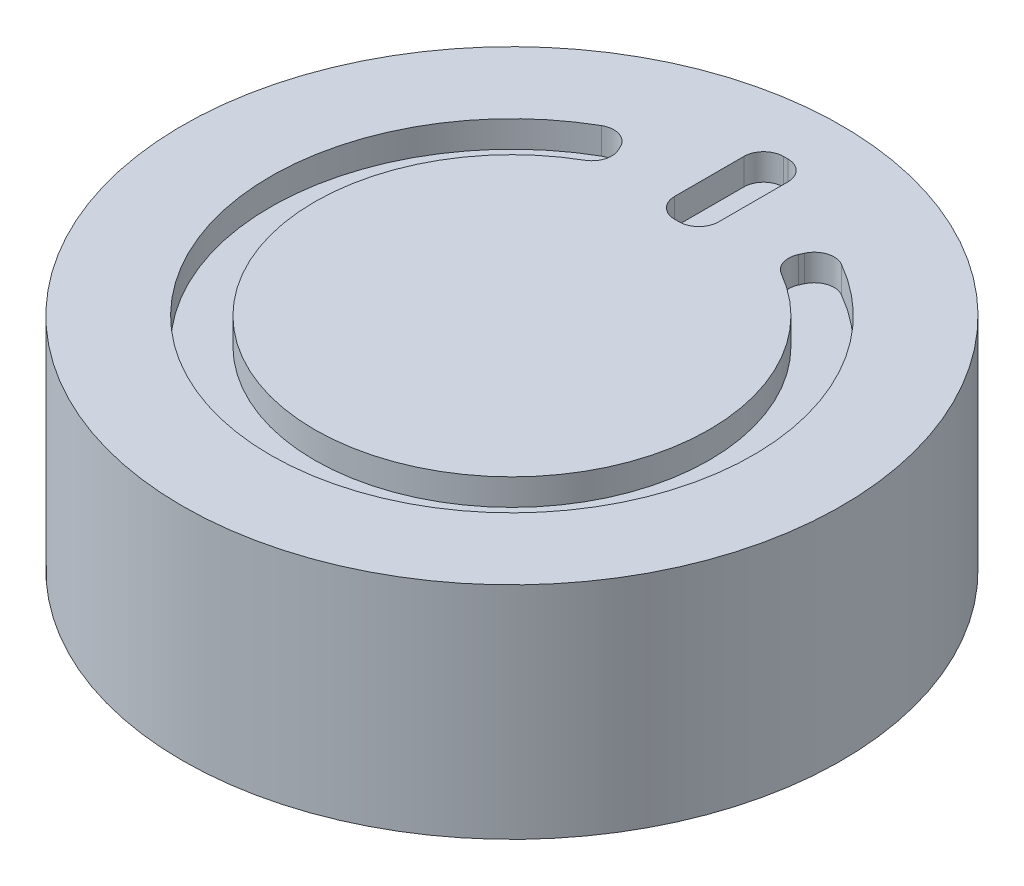
SolidWorks part; units mm, degrees
ref_plane "Front Plane" through (0, 0, 0) normal (0, 0, 1) x (1, 0, 0)
ref_plane "Top Plane" through (0, 0, 0) normal (0, 1, 0) x (1, 0, 0)
ref_plane "Right Plane" through (0, 0, 0) normal (1, 0, 0) x (0, 0, -1)
sketch "Sketch1" plane through (0, 0, 0) normal (0, 1, 0) x (1, 0, 0)
  circle A0 centre (0, 0) radius 14.95
  dimension "D1" = 29.9
extrude "Boss-Extrude1" add sketch "Sketch1" along normal blind 10
sketch "Sketch2" plane through (0, 10, 0) normal (0, 1, 0) x (1, 0, 0)
  line L0 (4.0952, 8.913) -> (4.179, 9.0955)
  line L1 (-0.1, 12.4204) -> (0.1, 12.4204)
  line L2 (-1, 11.5204) -> (-1, 8.3796)
  line L3 (-0.1, 7.4796) -> (0.1, 7.4796)
  line L4 (1, 11.5204) -> (1, 8.3796)
  line L5 (-1, 12.4204) -> (1, 7.4796) construction
  line L6 (-1, 7.4796) -> (1, 12.4204) construction
  line L7 (-4.0952, 8.913) -> (-4.179, 9.0955)
  arc A0 (1, 9.8996) -> (-1, 9.8996) centre (0, 0) ccw construction
  circle A1 centre (0, 0) radius 14.95 construction
  arc A2 (1, 10.9042) -> (-1, 10.9042) centre (0, 0) ccw
  arc A3 (1, 8.894) -> (-1, 8.894) centre (0, 0) ccw
  arc A4 (-5.4443, 9.5006) -> (5.4443, 9.5006) centre (0, 0) ccw
  arc A5 (-4.1541, 9.0413) -> (4.1541, 9.0413) centre (0, 0) ccw construction
  arc A6 (-4.4641, 7.7572) -> (4.4641, 7.7572) centre (0, 0) ccw
  arc A7 (1, 11.5204) -> (0.1, 12.4204) centre (0.1, 11.5204) ccw
  arc A8 (-0.1, 12.4204) -> (-1, 11.5204) centre (-0.1, 11.5204) ccw
  arc A9 (0.1, 7.4796) -> (1, 8.3796) centre (0.1, 8.3796) ccw
  arc A10 (-0.1, 7.4796) -> (-1, 8.3796) centre (-0.1, 8.3796) cw
  arc A11 (5.4443, 9.5006) -> (4.179, 9.0955) centre (4.9968, 8.7197) ccw
  arc A12 (4.4641, 7.7572) -> (4.0952, 8.913) centre (4.913, 8.5373) cw
  arc A13 (-4.4641, 7.7572) -> (-4.0952, 8.913) centre (-4.913, 8.5373) ccw
  arc A14 (-5.4443, 9.5006) -> (-4.179, 9.0955) centre (-4.9968, 8.7197) cw
  point P5 (0, 9.95)
  point P41 (-4.5717, 9.95)
  dimension "D1" = 5
  dimension "D2" = 4
  dimension "D3" = 6
  dimension "D4" = 0.9
  dimension "D5" = 2
extrude "Cut-Extrude1" cut sketch "Sketch2" against normal blind 1.2 contours A10 L3 A9 L4 A3 L2 | A3 L4 A2 L2 | L1 A8 L2 A2 L4 A7 | A6 A12 L0 A11 A4 A14 L7 A13
